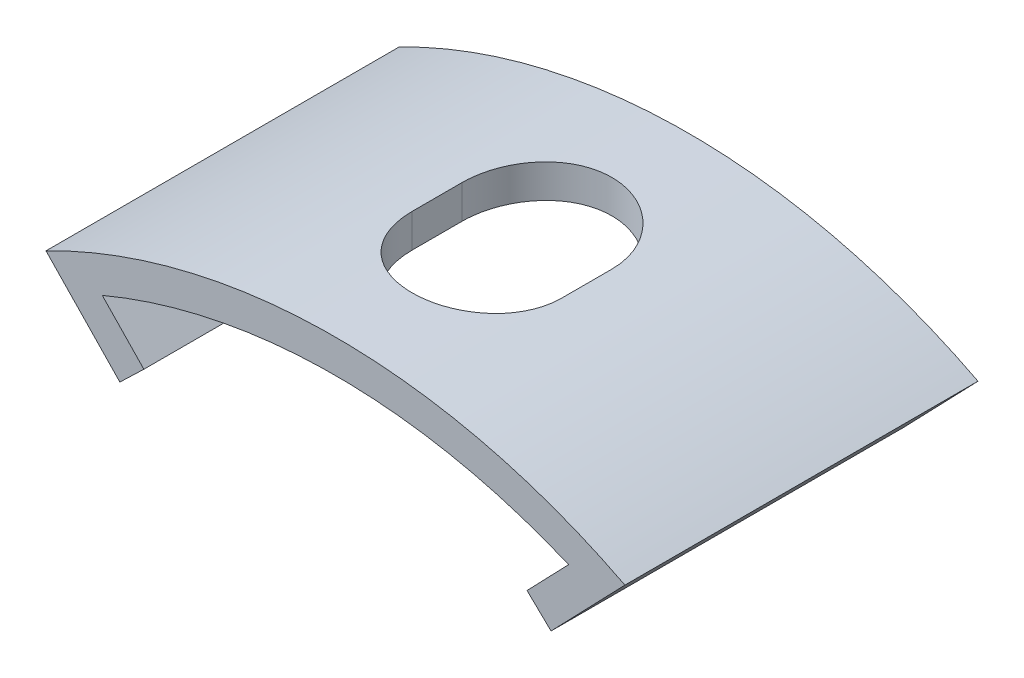
SolidWorks part; units mm, degrees
ref_plane "Face" through (0, 0, 0) normal (0, 0, 1) x (1, 0, 0)
ref_plane "Dessus" through (0, 0, 0) normal (0, 1, 0) x (1, 0, 0)
ref_plane "Droite" through (0, 0, 0) normal (1, 0, 0) x (0, 0, -1)
sketch "Esquisse1" plane through (0, 0, 0) normal (0, 0, 1) x (1, 0, 0)
  line L0 (0, 20.7893) -> (0, -13.3868) construction
  line L3 (5.7516, 15.2864) -> (0, 0) construction
  line L4 (0, 0) -> (21.7562, 16.3945) construction
  line L5 (-5.7516, 20.0495) -> (-5.7516, 13.0407) construction
  line L6 (-7, 16.5831) -> (-5.7516, 15.2864)
  line L7 (7, 16.5831) -> (5.7516, 15.2864)
  line L10 (0, 0) -> (26.587, 0) construction
  arc A1 (7, 16.5831) -> (-7, 16.5831) centre (0, 0) ccw
  dimension "D2" = 18
  dimension "D4" = 7
  dimension "D3" = 5.7516
  dimension "D6" = 53
  dimension "D11" = 1.8
extrude "Extru.-Mince1" add sketch "Esquisse1" along normal mid plane 10.6 thin
ref_plane "Plan1" through (0, 18, 0) normal (0, 1, 0) x (-1, 0, 0)
sketch "Esquisse2" plane through (0, 18, 0) normal (0, 1, 0) x (-1, 0, 0)
  line L0 (-10.5214, 0) -> (8.4741, 0) construction
  line L2 (-2.25, 0.75) -> (-2.25, -0.75)
  line L4 (2.25, 0.75) -> (2.25, -0.75)
  line L5 (0, 6.1591) -> (0, -4.8774) construction
  arc A0 (-2.25, 0.75) -> (2.25, 0.75) centre (0, 0.75) cw
  arc A1 (-2.25, -0.75) -> (2.25, -0.75) centre (0, -0.75) ccw
  dimension "D3" = 0.75
  dimension "D1" = 4.5
  dimension "D2" = 1.5
extrude "Enlèv. mat.-Extru.1" cut sketch "Esquisse2" along normal mid plane 11
